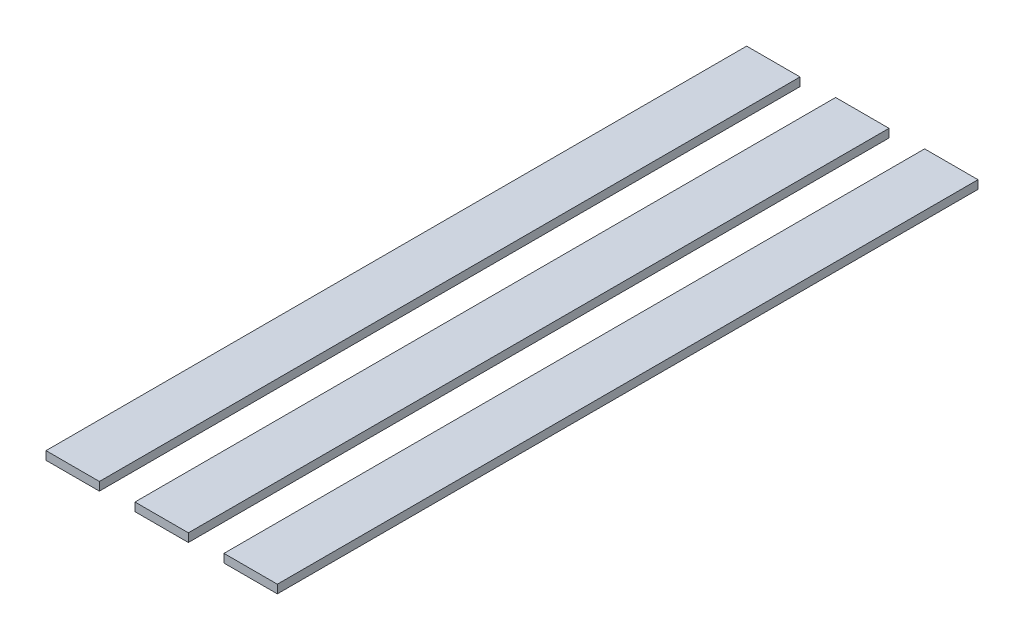
SolidWorks part; units mm, degrees
ref_plane "Alzado" through (0, 0, 0) normal (0, 0, 1) x (1, 0, 0)
ref_plane "Planta" through (0, 0, 0) normal (0, 1, 0) x (1, 0, 0)
ref_plane "Vista lateral" through (0, 0, 0) normal (1, 0, 0) x (0, 0, -1)
sketch "Croquis1" plane through (0, 0, 0) normal (0, 0, 1) x (1, 0, 0)
  line L1 (-19.05, -3) -> (19.05, -3)
  line L2 (-19.05, -3) -> (-19.05, 3)
  line L3 (-19.05, 3) -> (19.05, 3)
  line L4 (19.05, -3) -> (19.05, 3)
  line L5 (-19.05, -3) -> (19.05, 3) construction
  line L6 (-19.05, 3) -> (19.05, -3) construction
  line L7 (-82.55, -3) -> (-44.45, -3)
  line L8 (-82.55, -3) -> (-82.55, 3)
  line L9 (-82.55, 3) -> (-44.45, 3)
  line L10 (-44.45, -3) -> (-44.45, 3)
  line L11 (-82.55, -3) -> (-44.45, 3) construction
  line L12 (-82.55, 3) -> (-44.45, -3) construction
  line L13 (82.55, -3) -> (44.45, -3)
  line L14 (82.55, -3) -> (82.55, 3)
  line L15 (82.55, 3) -> (44.45, 3)
  line L16 (44.45, -3) -> (44.45, 3)
  line L17 (82.55, -3) -> (44.45, 3) construction
  line L18 (82.55, 3) -> (44.45, -3) construction
  point P0 (0, 0)
  point P6 (-63.5, 0)
  point P11 (63.5, 0)
  dimension "D1" = 38.1
  dimension "D2" = 6
  dimension "D3" = 25.4
  dimension "D4" = 25.4
  dimension "D5" = 38.1
  dimension "D6" = 38.1
extrude "Saliente-Extruir1" add sketch "Croquis1" along normal blind 500
